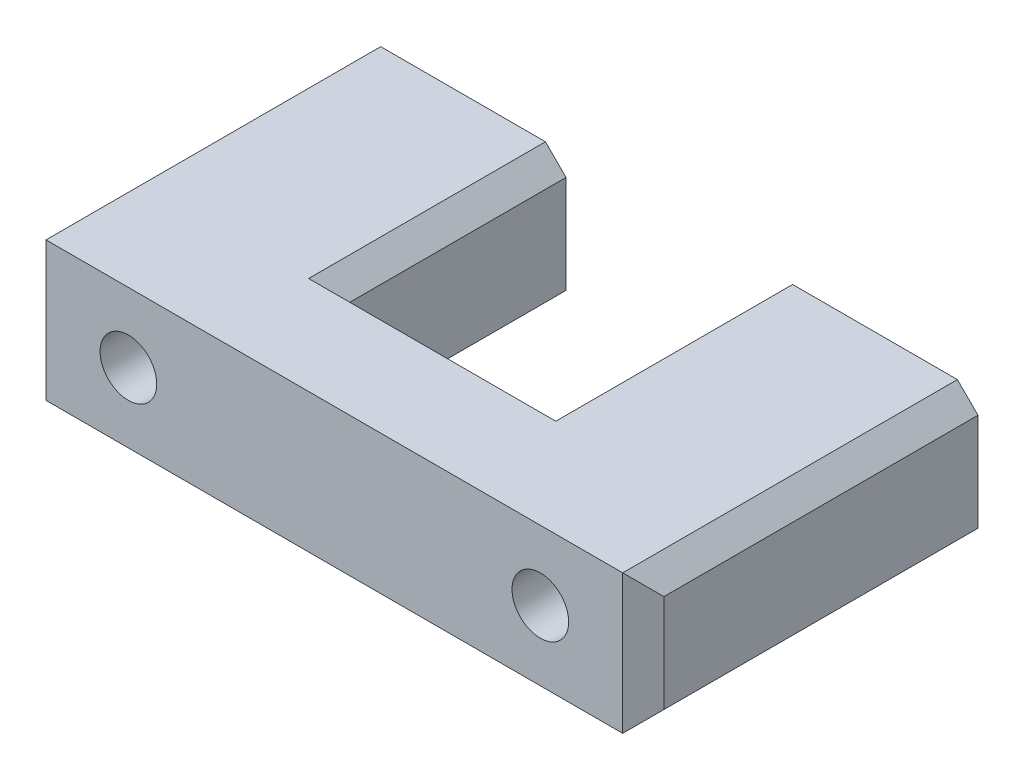
SolidWorks part; units mm, degrees
ref_plane "Front Plane" through (0, 0, 0) normal (1, 0, 0) x (0, 1, 0)
ref_plane "Top Plane" through (0, 0, 0) normal (0, 0, 1) x (0, 1, 0)
ref_plane "Right Plane" through (0, 0, 0) normal (0, 1, 0) x (-1, 0, 0)
sketch "Sketch1" plane through (0, 0, 0) normal (0, 0, 1) x (0, 1, 0)
  line L0 (0, 20) -> (0, -20) construction
  line L2 (-6.75, 30) -> (6.75, 30)
  line L3 (-6.75, 30) -> (-6.75, -30)
  line L4 (-6.75, -30) -> (6.75, -30)
  line L5 (6.75, 30) -> (6.75, -30)
  line L6 (-6.75, 30) -> (6.75, -30) construction
  line L7 (-6.75, -30) -> (6.75, 30) construction
  circle A0 centre (0, 20) radius 2.75
  circle A1 centre (0, -20) radius 2.75
  point P3 (0, 0)
  point P7 (0, 0)
  dimension "D1" = 5.5
  dimension "D2" = 40
  dimension "D3" = 13.5
  dimension "D4" = 10
extrude "Boss-Extrude1" add sketch "Sketch1" along normal blind 32.5
sketch "Sketch2" plane through (0, 6.75, 0) normal (0, 1, 0) x (-1, 0, 0)
  line L0 (-30, 0) -> (30, 0) construction
  line L2 (-10, 0) -> (10, 0)
  line L3 (-10, 0) -> (-10, 21)
  line L4 (-10, 21) -> (10, 21)
  line L5 (10, 0) -> (10, 21)
  point P0 (0, 0)
  point P7 (0, 0)
  point P8 (0, 0)
  dimension "D1" = 20
  dimension "D2" = 21
extrude "Cut-Extrude1" cut sketch "Sketch2" against normal through all
chamfer "Chamfer1" distance 2 angle 45 8 edges at (30, 0, 32.5) (30, -6.75, 16.25) (0, -6.75, 32.5) (-30, -6.75, 16.25) (-30, 0, 32.5) (30, 6.75, 16.25) (-30, 6.75, 16.25) (0, 6.75, 32.5)
chamfer "Chamfer2" distance 2 angle 45 6 edges at (-10, -6.75, 10.5) (10, -6.75, 10.5) (0, -6.75, 21) (-10, 6.75, 10.5) (0, 6.75, 21) (10, 6.75, 10.5)
